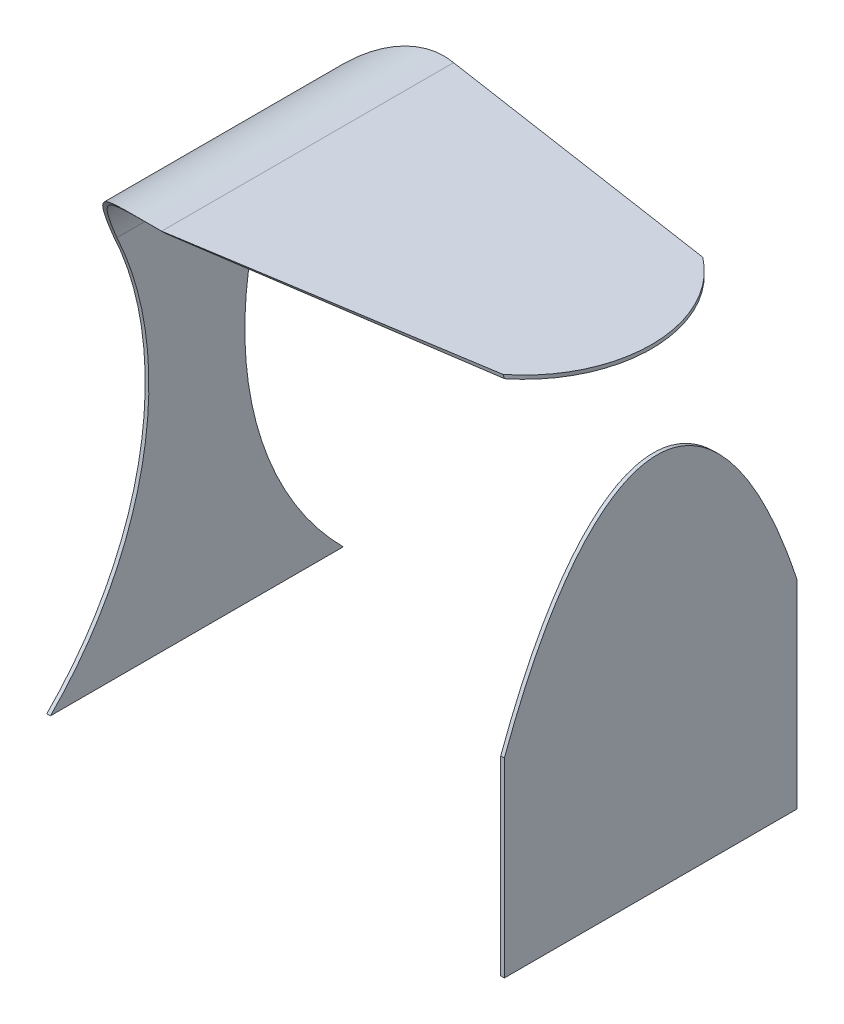
SolidWorks part; units mm, degrees
ref_plane "Front Plane" through (0, 0, 0) normal (0, 0, 1) x (1, 0, 0)
ref_plane "Top Plane" through (0, 0, 0) normal (0, 1, 0) x (1, 0, 0)
ref_plane "Right Plane" through (0, 0, 0) normal (1, 0, 0) x (0, 0, -1)
sketch "Sketch1" plane through (0, 0, 0) normal (0, 0, 1) x (1, 0, 0)
  line L0 (0, 0) -> (0, 100)
  line L1 (0, 0) -> (0, -58.1363)
  line L2 (250, 0) -> (250, 100)
  line L3 (250, 0) -> (250, -58.1363)
  line L4 (0, -58.1363) -> (0, -108.1363)
  line L5 (250, -58.1363) -> (250, -108.1363)
  line L10 (62.5, 151.318) -> (187.5, 151.318)
  arc A0 (0, 100) -> (62.5, 151.318) centre (56.909, 94.409) cw
  arc A1 (187.5, 151.318) -> (250, 100) centre (193.091, 94.409) cw
extrude "Extrude-Thin3" add sketch "Sketch1" along normal blind 160 thin
sketch "Sketch2" plane through (0, 151.318, 0) normal (0, 1, 0) x (1, 0, 0)
  line L1 (62.5, 0) -> (250, 0)
  line L2 (62.5, 0) -> (62.5, -160)
  line L3 (62.5, -160) -> (250, -160)
  line L4 (250, 0) -> (250, -160)
extrude "Cut-Extrude1" cut sketch "Sketch2" against normal blind 50
sketch "Sketch3" plane through (0, 151.318, 0) normal (0, -1, 0) x (1, 0, 0)
  line L1 (172.2827, 163.6228) -> (213.6212, 163.6228)
  line L2 (172.2827, 163.6228) -> (172.2827, -11.188)
  line L3 (172.2827, -11.188) -> (213.6212, -11.188)
  line L4 (213.6212, 163.6228) -> (213.6212, -11.188)
extrude "Cut-Extrude2" cut sketch "Sketch3" against normal blind 50
sketch "Sketch4" plane through (0, 0, 0) normal (-1, 0, 0) x (0, 0, 1)
  line L2 (0, -108.1363) -> (0, 100) construction
  line L3 (0, 100) -> (0, -108.1363)
  line L4 (160, 100) -> (160, -108.1363)
  arc A0 (0, 100) -> (0, -108.1363) centre (-104.0682, -4.0682) cw
  arc A1 (160, 100) -> (160, -108.1363) centre (264.0682, -4.0682) ccw
extrude "Cut-Extrude3" cut sketch "Sketch4" against normal blind 50
sketch "Sketch10" plane through (0, 0, 0) normal (-1, 0, 0) x (0, 0, 1)
  line L0 (0, 151.592) -> (0, -108.1363)
  line L1 (160, 151.592) -> (160, -108.1363)
  arc A0 (160, 151.592) -> (160, -108.1363) centre (289.8642, 21.7278) ccw
extrude "Cut-Extrude4" cut sketch "Sketch10" against normal blind 76 contours L1 A0
sketch "Sketch11" plane through (0, 0, 0) normal (-1, 0, 0) x (0, 0, 1)
  line L0 (0, 151.592) -> (0, -108.1363)
  arc A0 (0, -108.1363) -> (0, 151.592) centre (-129.8642, 21.7278) ccw
extrude "Cut-Extrude5" cut sketch "Sketch11" against normal blind 76
sketch "Sketch12" plane through (250, 0, 0) normal (1, 0, 0) x (0, 0, -1)
  line L0 (-160, 100) -> (-160, -108.1363) construction
  line L1 (-160, -4.0682) -> (-160, 100)
  line L2 (-160, 100) -> (-160, 129.7514)
  line L3 (-160, 129.7514) -> (0, 129.7514)
  line L4 (0, 129.7514) -> (0, 0)
  conic Q0 (-160, -4.0682) -> (0, 0) control (-74.3506, 228.5591) rho 0.432306
extrude "Cut-Extrude6" cut sketch "Sketch12" against normal blind 76
ref_plane "Plane1" through (250, 0, 0) normal (1, 0, 0) x (0, 0, -1)
sketch "Sketch15" plane through (250, 0, 0) normal (1, 0, 0) x (0, 0, -1)
  line L0 (-157.7652, 149.318) -> (-2.2348, 149.318) construction
  line L1 (-130.0308, 149.318) -> (-28.3491, 149.318)
  line L2 (-130.0308, 149.318) -> (-130.0308, 151.318)
  line L3 (-130.0308, 151.318) -> (-28.3491, 151.318)
  line L4 (-28.3491, 149.318) -> (-28.3491, 151.318)
  line L5 (-159.7266, 151.318) -> (-0.2734, 151.318) construction
loft "Loft2" add profiles "Sketch15" section face at (62.5, 150.3199, 80) section "Sketch15"
sketch "Sketch16" plane through (0, 151.318, 0) normal (0, 1, 0) x (1, 0, 0)
  line L0 (62.5, -0.2734) -> (250, -28.3491) construction
  line L1 (62.5, -159.7266) -> (250, -130.0308) construction
  line L2 (156.25, -14.3112) -> (176.822, 28.4323)
  line L3 (176.822, 28.4323) -> (259.5533, -32.5907)
  line L4 (259.5533, -32.5907) -> (263.1836, -157.3847)
  line L5 (263.1836, -157.3847) -> (159.9719, -160.3871)
  line L6 (159.9719, -160.3871) -> (156.25, -144.8787)
  arc A0 (156.25, -14.3112) -> (156.25, -144.8787) centre (180.3945, -79.595) cw
extrude "Cut-Extrude7" cut sketch "Sketch16" against normal blind 28
